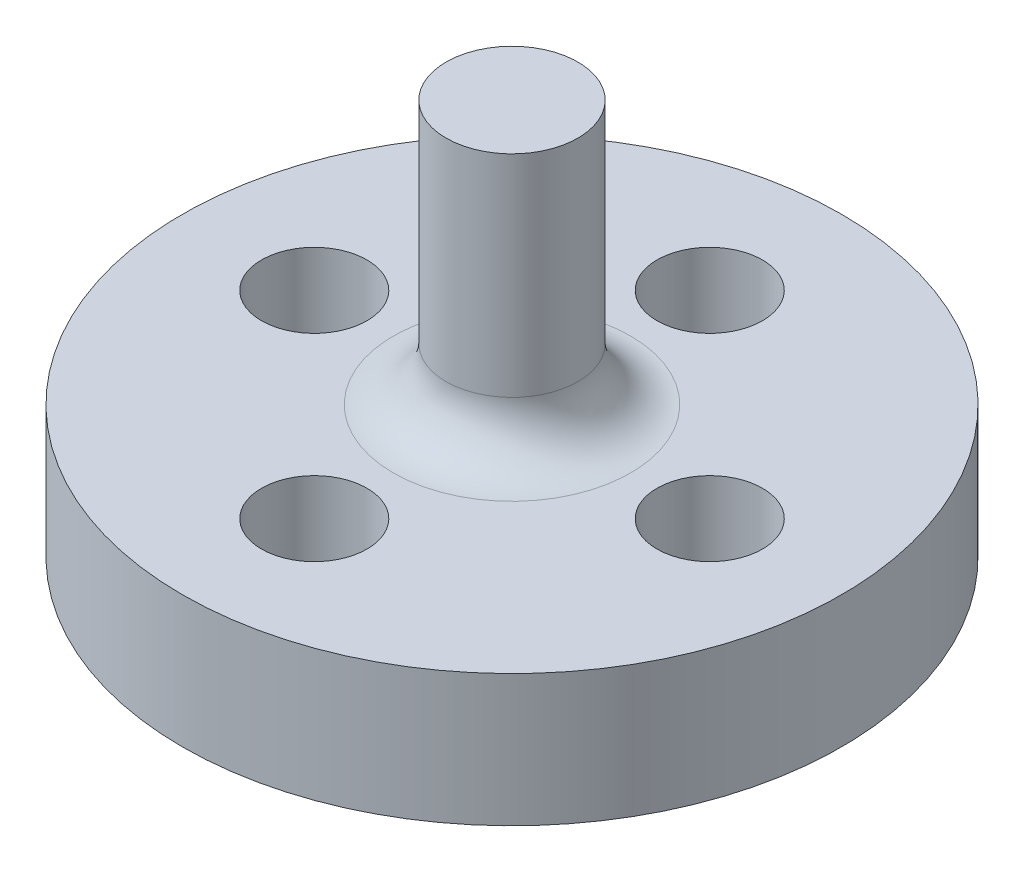
SolidWorks part; units mm, degrees
ref_plane "Front Plane" through (0, 0, 0) normal (0, 0, 1) x (1, 0, 0)
ref_plane "Top Plane" through (0, 0, 0) normal (0, 1, 0) x (1, 0, 0)
ref_plane "Right Plane" through (0, 0, 0) normal (1, 0, 0) x (0, 0, -1)
sketch "Sketch1" plane through (0, 0, 0) normal (0, 1, 0) x (1, 0, 0)
  line L0 (0, -7.5) -> (0, 7.5)
  line L1 (-7.5, 0) -> (7.5, 0)
  circle A0 centre (0, 0) radius 12.5
  circle A1 centre (-7.5, 0) radius 2
  circle A2 centre (0, 7.5) radius 2
  circle A3 centre (7.5, 0) radius 2
  circle A4 centre (0, -7.5) radius 2
  point P6 (0, 0)
  point P9 (0, 0)
  dimension "D1" = 25
  dimension "D4" = 4
  dimension "D5" = 4
  dimension "D6" = 4
  dimension "D7" = 4
  dimension "D2" = 15
  dimension "D3" = 15
extrude "Boss-Extrude1" add sketch "Sketch1" along normal blind 5
sketch "Sketch2" plane through (0, 5, 0) normal (0, 1, 0) x (1, 0, 0)
  circle A0 centre (0, 0) radius 2.5
  dimension "D1" = 5
extrude "Boss-Extrude2" add sketch "Sketch2" along normal blind 10
sketch "Sketch3" plane through (0, 0, 0) normal (0, -1, 0) x (1, 0, 0)
  circle A0 centre (0, 0) radius 5
  dimension "D1" = 10
extrude "Cut-Extrude1" cut sketch "Sketch3" against normal blind 2
fillet "Fillet2" radius 2 1 edges at (0, 5, 2.5)
